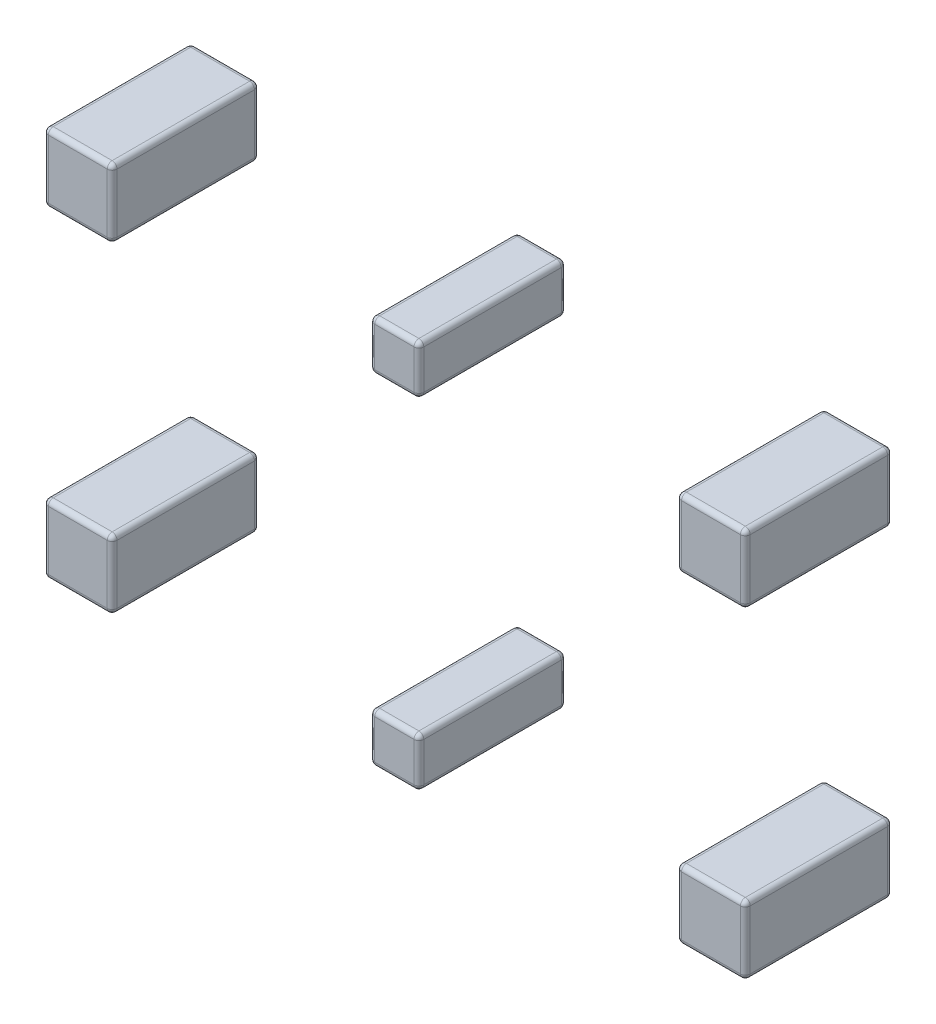
SolidWorks part; units mm, degrees
ref_plane "Płaszczyzna przednia" through (0, 0, 0) normal (0, 0, 1) x (1, 0, 0)
ref_plane "Płaszczyzna górna" through (0, 0, 0) normal (0, 1, 0) x (1, 0, 0)
ref_plane "Płaszczyzna prawa" through (0, 0, 0) normal (1, 0, 0) x (0, 0, -1)
ref_plane "Płaszczyzna1" through (0, 0, 193) normal (0, 0, -1) x (-1, 0, 0)
sketch "Szkic1" plane through (0, 0, 193) normal (0, 0, -1) x (-1, 0, 0)
  line L1 (-1083.7522, 514.8731) -> (-1363.7522, 514.8731)
  line L2 (-1083.7522, 514.8731) -> (-1083.7522, 794.8731)
  line L3 (-1083.7522, 794.8731) -> (-1363.7522, 794.8731)
  line L4 (-1363.7522, 514.8731) -> (-1363.7522, 794.8731)
  line L5 (-33.7522, 592.3731) -> (166.2478, 592.3731)
  line L6 (-33.7522, 592.3731) -> (-33.7522, 792.3731)
  line L7 (-33.7522, 792.3731) -> (166.2478, 792.3731)
  line L8 (166.2478, 592.3731) -> (166.2478, 792.3731)
  line L9 (1496.2478, 794.8731) -> (1216.2478, 794.8731)
  line L10 (1496.2478, 794.8731) -> (1496.2478, 514.8731)
  line L11 (1496.2478, 514.8731) -> (1216.2478, 514.8731)
  line L12 (1216.2478, 794.8731) -> (1216.2478, 514.8731)
  line L13 (1496.2478, -795.1269) -> (1216.2478, -795.1269)
  line L14 (1496.2478, -795.1269) -> (1496.2478, -515.1269)
  line L15 (1496.2478, -515.1269) -> (1216.2478, -515.1269)
  line L16 (1216.2478, -795.1269) -> (1216.2478, -515.1269)
  line L17 (-33.7522, -792.6269) -> (166.2478, -792.6269)
  line L18 (-33.7522, -792.6269) -> (-33.7522, -592.6269)
  line L19 (-33.7522, -592.6269) -> (166.2478, -592.6269)
  line L20 (166.2478, -792.6269) -> (166.2478, -592.6269)
  line L21 (-1083.7522, -795.1269) -> (-1363.7522, -795.1269)
  line L22 (-1083.7522, -795.1269) -> (-1083.7522, -515.1269)
  line L23 (-1083.7522, -515.1269) -> (-1363.7522, -515.1269)
  line L24 (-1363.7522, -795.1269) -> (-1363.7522, -515.1269)
extrude "Dodanie-wyciągnięcie1" add sketch "Szkic1" along normal blind 600
fillet "Zaokrąglenie1" radius 20 12 edges at (1363.7522, 654.8731, -407) (1363.7522, 654.8731, 193) (1363.7522, 514.8731, -107) (1223.7522, 514.8731, -407) (1223.7522, 514.8731, 193) (1083.7522, 514.8731, -107) (1083.7522, 654.8731, -407) (1083.7522, 654.8731, 193) (1083.7522, 794.8731, -107) (1223.7522, 794.8731, -407) (1223.7522, 794.8731, 193) (1363.7522, 794.8731, -107)
fillet "Zaokrąglenie2" radius 20 12 edges at (1083.7522, -655.1269, -407) (1083.7522, -655.1269, 193) (1223.7522, -795.1269, -407) (1083.7522, -795.1269, -107) (1223.7522, -795.1269, 193) (1363.7522, -655.1269, -407) (1363.7522, -795.1269, -107) (1363.7522, -655.1269, 193) (1083.7522, -515.1269, -107) (1223.7522, -515.1269, -407) (1363.7522, -515.1269, -107) (1223.7522, -515.1269, 193)
fillet "Zaokrąglenie3" radius 20 12 edges at (-66.2478, -592.6269, -407) (-66.2478, -592.6269, 193) (33.7522, -592.6269, -107) (33.7522, -692.6269, -407) (33.7522, -692.6269, 193) (-166.2478, -692.6269, -407) (-166.2478, -592.6269, -107) (-166.2478, -692.6269, 193) (33.7522, -792.6269, -107) (-66.2478, -792.6269, -407) (-166.2478, -792.6269, -107) (-66.2478, -792.6269, 193)
fillet "Zaokrąglenie4" radius 20 12 edges at (-1216.2478, -655.1269, -407) (-1216.2478, -655.1269, 193) (-1216.2478, -795.1269, -107) (-1356.2478, -795.1269, -407) (-1356.2478, -795.1269, 193) (-1496.2478, -795.1269, -107) (-1496.2478, -655.1269, -407) (-1496.2478, -655.1269, 193) (-1496.2478, -515.1269, -107) (-1356.2478, -515.1269, -407) (-1216.2478, -515.1269, -107) (-1356.2478, -515.1269, 193)
fillet "Zaokrąglenie5" radius 20 12 edges at (-66.2478, 592.3731, -407) (-66.2478, 592.3731, 193) (-166.2478, 592.3731, -107) (-166.2478, 692.3731, -407) (-166.2478, 692.3731, 193) (33.7522, 692.3731, -407) (33.7522, 592.3731, -107) (33.7522, 692.3731, 193) (-166.2478, 792.3731, -107) (-66.2478, 792.3731, -407) (33.7522, 792.3731, -107) (-66.2478, 792.3731, 193)
fillet "Zaokrąglenie6" radius 20 12 edges at (-1356.2478, 794.8731, -407) (-1356.2478, 794.8731, 193) (-1496.2478, 654.8731, -407) (-1496.2478, 794.8731, -107) (-1496.2478, 654.8731, 193) (-1216.2478, 794.8731, -107) (-1216.2478, 654.8731, -407) (-1216.2478, 654.8731, 193) (-1216.2478, 514.8731, -107) (-1356.2478, 514.8731, -407) (-1496.2478, 514.8731, -107) (-1356.2478, 514.8731, 193)
